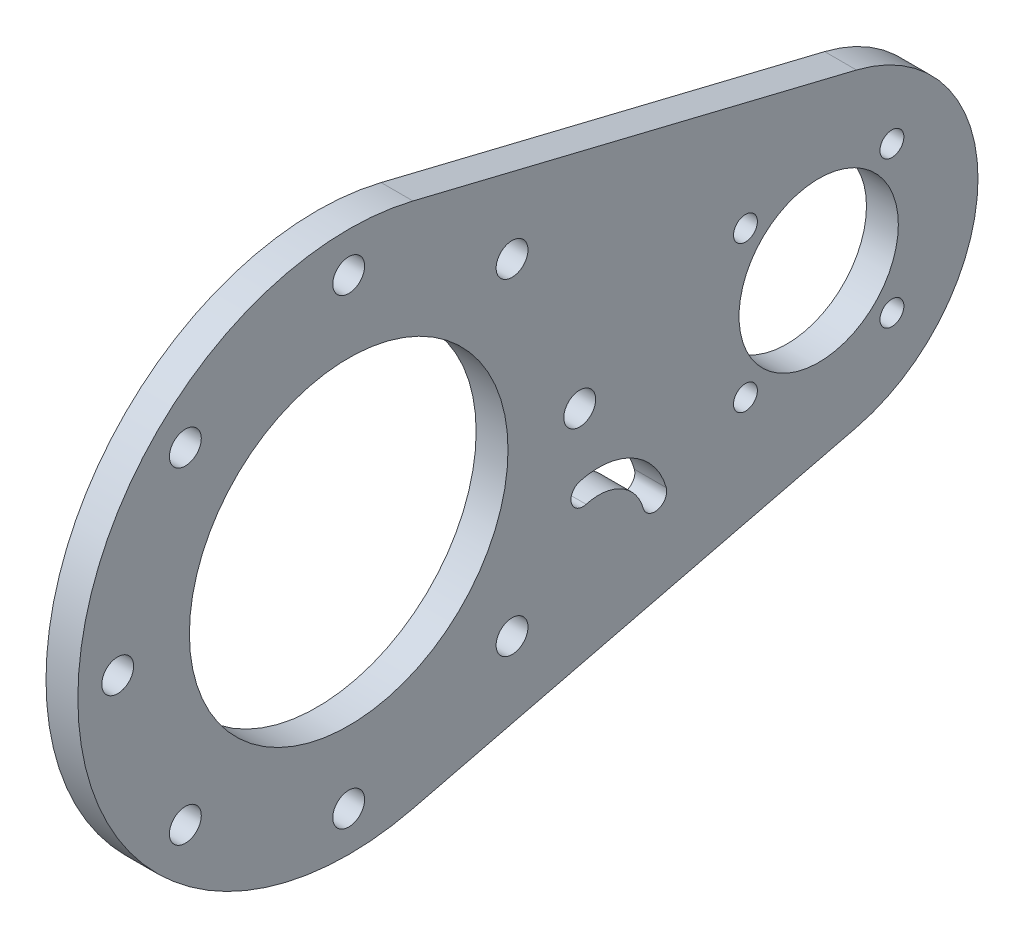
SolidWorks part; units mm, degrees
ref_plane "Front Plane" through (0, 0, 0) normal (0, 0, 1) x (1, 0, 0)
ref_plane "Top Plane" through (0, 0, 0) normal (0, 1, 0) x (1, 0, 0)
ref_plane "Right Plane" through (0, 0, 0) normal (1, 0, 0) x (0, 0, -1)
sketch "Sketch1" plane through (0, 0, 0) normal (1, 0, 0) x (0, 0, -1)
  line L0 (0, 0) -> (59, 0) construction
  line L1 (8.0678, 33.0289) -> (63.7458, 19.4288)
  line L2 (8.0678, -33.0289) -> (63.7458, -19.4288)
  line L3 (46, 0) -> (72, 0) construction
  line L4 (59, 0) -> (49.8076, 9.1924) construction
  arc A1 (63.7458, -19.4288) -> (63.7458, 19.4288) centre (59, 0) ccw
  arc A2 (8.0678, 33.0289) -> (8.0678, -33.0289) centre (0, 0) ccw
  circle A3 centre (0, 0) radius 29 construction
  circle A4 centre (59, 0) radius 10
  circle A5 centre (0, 0) radius 20
  circle A6 centre (0, 29) radius 2
  circle A7 centre (20.5061, 20.5061) radius 2
  circle A8 centre (29, 0) radius 2
  circle A9 centre (20.5061, -20.5061) radius 2
  circle A10 centre (0, -29) radius 2
  circle A11 centre (-20.5061, -20.5061) radius 2
  circle A12 centre (-29, 0) radius 2
  circle A13 centre (-20.5061, 20.5061) radius 2
  circle A14 centre (59, 0) radius 13 construction
  circle A15 centre (49.8076, 9.1924) radius 1.5
  circle A19 centre (68.1924, 9.1924) radius 1.5
  circle A20 centre (68.1924, -9.1924) radius 1.5
  circle A21 centre (49.8076, -9.1924) radius 1.5
  point P3 (75, 0)
  point P30 (0, 0)
  point P41 (59, 0)
  point P44 (59, 0)
  dimension "D1" = 20
  dimension "D3" = 68
  dimension "D4" = 58
  dimension "D5" = 20
  dimension "D6" = 40
  dimension "D7" = 4
  dimension "D9" = 26
  dimension "D11" = 3
  dimension "D2" = 59
  dimension "D10" = 45
  dimension "D8" = 8
  dimension "D12" = 4
extrude "Boss-Extrude1" add sketch "Sketch1" along normal blind 4
sketch "Sketch2" plane through (0, 0, 0) normal (-1, 0, 0) x (0, 0, 1)
  arc A0 (-38.4209, -14.4398) -> (-29.4005, -9.3736) centre (-31.3776, -16.4169) cw construction
  arc A1 (-28.9951, -7.9294) -> (-39.8651, -14.0344) centre (-31.3776, -16.4169) ccw
  arc A2 (-29.8059, -10.8178) -> (-36.9767, -14.8452) centre (-31.3776, -16.4169) ccw
  arc A3 (-29.8059, -10.8178) -> (-28.9951, -7.9294) centre (-29.4005, -9.3736) ccw
  arc A4 (-39.8651, -14.0344) -> (-36.9767, -14.8452) centre (-38.4209, -14.4398) ccw
  point P3 (-34.96, -10.0385)
  dimension "D1" = 1.5
extrude "Cut-Extrude1" cut sketch "Sketch2" against normal blind 10
sketch "Bend-Lines1" [suppressed] plane through (0, 0, 0) normal (0, 1, 0) x (1, 0, 0)
sketch "Bounding-Box1" [suppressed] plane through (0, 0, 0) normal (0, 1, 0) x (1, 0, 0)
